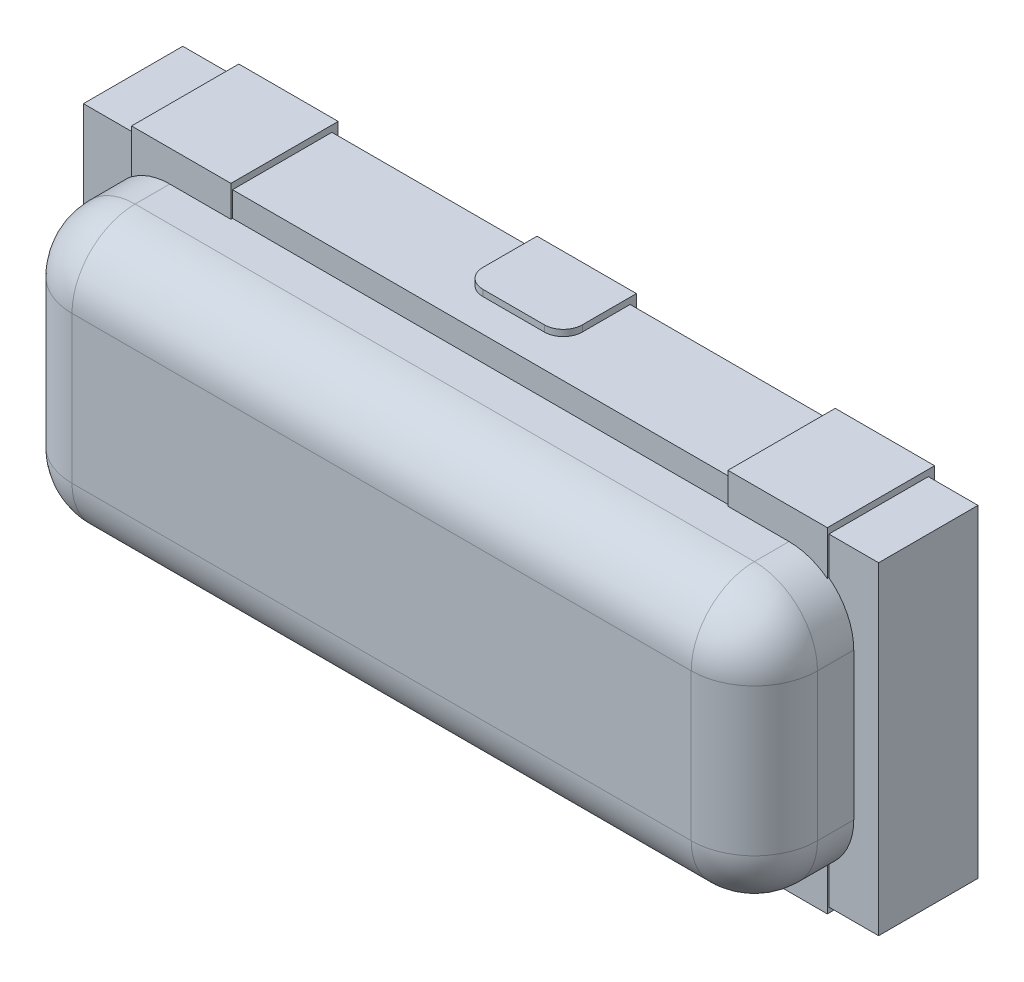
SolidWorks part; units mm, degrees
ref_plane "Front Plane" through (0, 0, 0) normal (0, 0, 1) x (1, 0, 0)
ref_plane "Top Plane" through (0, 0, 0) normal (0, 1, 0) x (1, 0, 0)
ref_plane "Right Plane" through (0, 0, 0) normal (1, 0, 0) x (0, 0, -1)
sketch "Sketch1" plane through (0, 0, 0) normal (0, 0, 1) x (1, 0, 0)
  line L1 (0, 0) -> (3.2, 0)
  line L2 (0, 0) -> (0, 1.3)
  line L3 (0, 1.3) -> (3.2, 1.3)
  line L4 (3.2, 0) -> (3.2, 1.3)
  dimension "D1" = 3.2
  dimension "D2" = 1.3
extrude "Boss-Extrude1" add sketch "Sketch1" along normal blind 0.4
sketch "Sketch2" plane through (0, 0, 0.4) normal (0, 0, 1) x (1, 0, 0)
  line L0 (3.2, 1.3) -> (0, 1.3) construction
  line L1 (0.1, 1.2) -> (3.1, 1.2)
  line L2 (0.1, 1.2) -> (0.1, 0.1)
  line L3 (0.1, 0.1) -> (3.1, 0.1)
  line L4 (3.1, 1.2) -> (3.1, 0.1)
  line L5 (0, 1.3) -> (0, 0) construction
  dimension "D1" = 1.1
  dimension "D2" = 0.1
  dimension "D3" = 0.1
  dimension "D4" = 3
extrude "Boss-Extrude2" add sketch "Sketch2" along normal blind 0.4
fillet "Fillet1" radius 0.254 8 edges at (1.6, 1.2, 0.8) (0.1, 0.65, 0.8) (1.6, 0.1, 0.8) (3.1, 0.65, 0.8) (3.1, 1.2, 0.6) (3.1, 0.1, 0.6) (0.1, 1.2, 0.6) (0.1, 0.1, 0.6)
sketch "Sketch3" plane through (0, 0, 0) normal (0, 0, -1) x (-1, 0, 0)
  line L0 (0, 0) -> (-3.2, 0) construction
  line L1 (-0.2, 0) -> (-0.6, 0)
  line L2 (-0.2, 0) -> (-0.2, 1.3)
  line L3 (-0.2, 1.3) -> (-0.6, 1.3)
  line L4 (-0.6, 0) -> (-0.6, 1.3)
  line L5 (-3.2, 1.3) -> (0, 1.3) construction
  line L7 (-2.6, 0) -> (-3, 0)
  line L8 (-2.6, 0) -> (-2.6, 1.3)
  line L9 (-2.6, 1.3) -> (-3, 1.3)
  line L10 (-3, 0) -> (-3, 1.3)
  line L11 (-1.4, 0) -> (-1.8, 0)
  line L12 (-1.4, 0) -> (-1.4, 1.3)
  line L13 (-1.4, 1.3) -> (-1.8, 1.3)
  line L14 (-1.8, 0) -> (-1.8, 1.3)
  line L15 (-2.8, 1.3) -> (-2.8, 0) construction
  line L16 (-3.2, 0) -> (-3.2, 1.3) construction
  line L17 (-1.6, 1.3) -> (-1.6, 0) construction
  line L19 (-0.4, 1.3) -> (-0.4, 0) construction
  dimension "D1" = 0.4
  dimension "D2" = 0.4
  dimension "D3" = 0.4
  dimension "D4" = 0.4
  dimension "D5" = 1.2
  dimension "D6" = 1.2
extrude "Boss-Extrude3" add sketch "Sketch3" along normal blind 0.0254
sketch "Sketch4" plane through (0, 1.3, 0) normal (0, 1, 0) x (1, 0, 0)
  line L0 (1.4, 0.0254) -> (1.4, -0.1925)
  line L1 (0.2, 0.0254) -> (0.6, 0.0254)
  line L2 (0.2, 0.0254) -> (0.2, -0.4064)
  line L3 (0.2, -0.4064) -> (0.6, -0.4064)
  line L4 (0.6, 0.0254) -> (0.6, -0.4064)
  line L5 (1.4, 0.0254) -> (1.8, 0.0254)
  line L6 (1.4762, -0.2687) -> (1.7238, -0.2687)
  line L7 (1.8, -0.1925) -> (1.8, 0.0254)
  line L9 (2.6, 0.0254) -> (3, 0.0254)
  line L10 (2.6, 0.0254) -> (2.6, -0.4064)
  line L11 (2.6, -0.4064) -> (3, -0.4064)
  line L12 (3, 0.0254) -> (3, -0.4064)
  arc A0 (1.7238, -0.2687) -> (1.8, -0.1925) centre (1.7238, -0.1925) ccw
  arc A1 (1.4762, -0.2687) -> (1.4, -0.1925) centre (1.4762, -0.1925) cw
  dimension "D3" = 0.0762
  dimension "D1" = 0.4318
  dimension "D2" = 0.4
  dimension "D4" = 0.2941
extrude "Boss-Extrude4" add sketch "Sketch4" along normal blind 0.0254 and the other way blind 1.3208
